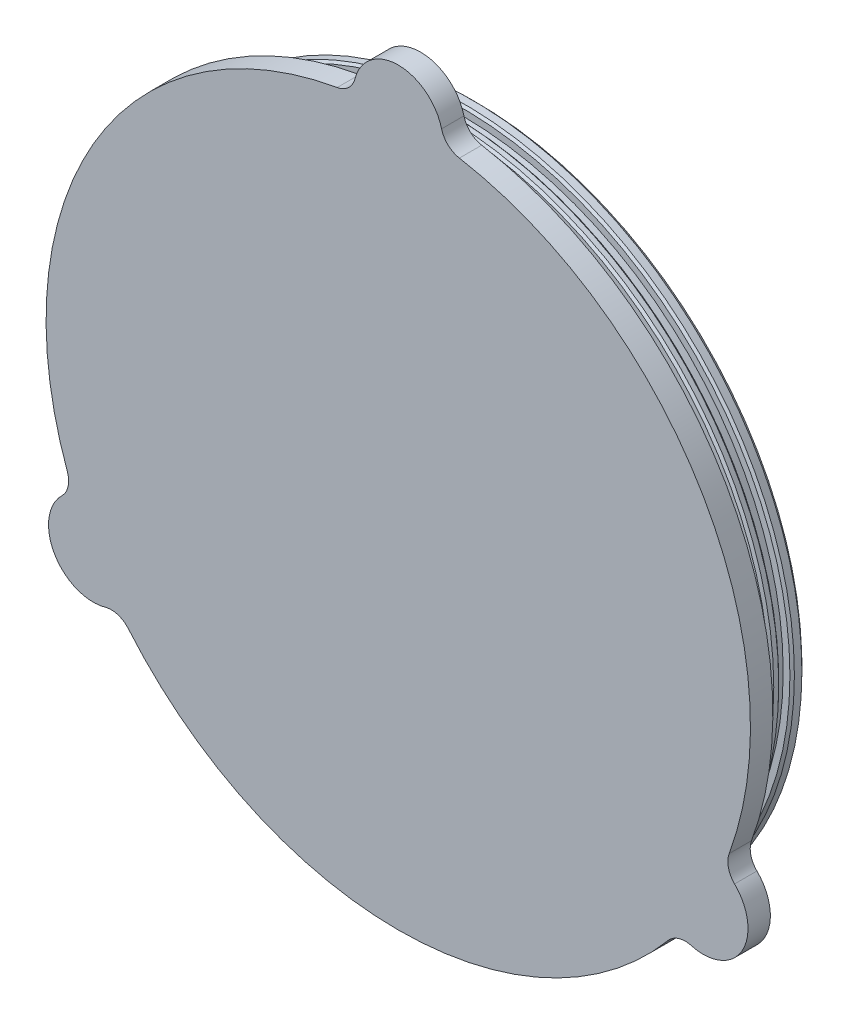
SolidWorks part; units mm, degrees
material "6061-T6 (SS)"
ref_plane "Front Plane" through (0, 0, 0) normal (0, 0, 1) x (1, 0, 0)
ref_plane "Top Plane" through (0, 0, 0) normal (0, 1, 0) x (1, 0, 0)
ref_plane "Right Plane" through (0, 0, 0) normal (1, 0, 0) x (0, 0, -1)
sketch "Sketch1" plane through (0, 0, 0) normal (0, 0, 1) x (1, 0, 0)
  circle A0 centre (0, 0) radius 100.0125
  dimension "D1" = 200.025
extrude "Extrude1" add sketch "Sketch1" along normal blind 6.35
sketch "Sketch2" plane through (0, 0, 0) normal (0, 0, -1) x (-1, 0, 0)
  circle A0 centre (0, 0) radius 93.6625
  dimension "D1" = 187.325
extrude "Extrude2" add sketch "Sketch2" along normal blind 15.875
sketch "Sketch3" plane through (0, 0, -15.875) normal (0, 0, -1) x (-1, 0, 0)
  circle A0 centre (0, 0) radius 87.3125
  dimension "D1" = 174.625
extrude "Cut-Extrude1" cut sketch "Sketch3" against normal blind 15.875
sketch "Sketch4" plane through (0, 0, 0) normal (1, 0, 0) x (0, 0, -1)
  line L0 (15.875, 93.6625) -> (0, 93.6625) construction
  line L1 (2.8084, 93.6625) -> (5.9834, 93.6625)
  line L2 (2.8084, 93.6625) -> (2.8084, 91.1225)
  line L3 (2.8084, 91.1225) -> (5.9834, 91.1225)
  line L4 (5.9834, 93.6625) -> (5.9834, 91.1225)
  line L5 (0, 0) -> (42.3826, 0) construction
  line L6 (8.6645, 93.6625) -> (11.8395, 93.6625)
  line L7 (8.6645, 93.6625) -> (8.6645, 91.1225)
  line L8 (8.6645, 91.1225) -> (11.8395, 91.1225)
  line L9 (11.8395, 93.6625) -> (11.8395, 91.1225)
  line L10 (0, -100.0125) -> (0, 100.0125) construction
  dimension "D1" = 2.54
  dimension "D2" = 3.175
  dimension "D3" = 2.8084
  dimension "D4" = 2.6811
revolve "Cut-Revolve1" cut sketch "Sketch4" angle 360 about L5
chamfer "Chamfer1" distance 1.27 angle 45 1 edges at (-93.6625, 0, -15.875)
sketch "Sketch8" plane through (0, 0, 6.35) normal (0, 0, 1) x (1, 0, 0)
  line L0 (0, 0) -> (86.6134, -50.0063) construction
  line L1 (0, 0) -> (-86.6134, -50.0063) construction
  line L2 (0, 0) -> (0, 100.0125) construction
  circle A0 centre (0, 0) radius 100.0125 construction
  arc A1 (-12.6744, 99.2062) -> (12.6744, 99.2062) centre (0, 100.0125) cw
  arc A2 (92.2522, -38.6267) -> (79.5779, -60.5794) centre (86.6134, -50.0063) cw
  arc A3 (-92.2522, -38.6267) -> (-79.5779, -60.5794) centre (-86.6134, -50.0063) ccw
  arc A4 (-12.6744, 99.2062) -> (12.6744, 99.2062) centre (0, 0) cw
  arc A5 (92.2522, -38.6267) -> (79.5779, -60.5794) centre (0, 0) cw
  arc A6 (-92.2522, -38.6267) -> (-79.5779, -60.5794) centre (0, 0) ccw
  dimension "D1" = 12.7
  dimension "D2" = 12.7
  dimension "D3" = 12.7
  dimension "D4" = 120
  dimension "D5" = 120
extrude "Extrude3" add sketch "Sketch8" against normal up to surface (6.35 mm away) up to face at (100.0125, 0, 0)
chamfer "Chamfer2" distance 0.635 angle 45 4 edges at (93.6625, 0, -2.8084) (93.6625, 0, -5.9834) (93.6625, 0, -8.6645) (93.6625, 0, -11.8395)
fillet "Fillet1" radius 6.35 6 edges at (92.2522, -38.6267, 3.175) (79.5779, -60.5794, 3.175) (-12.6744, 99.2062, 3.175) (12.6744, 99.2062, 3.175) (-79.5779, -60.5794, 3.175) (-92.2522, -38.6267, 3.175)
